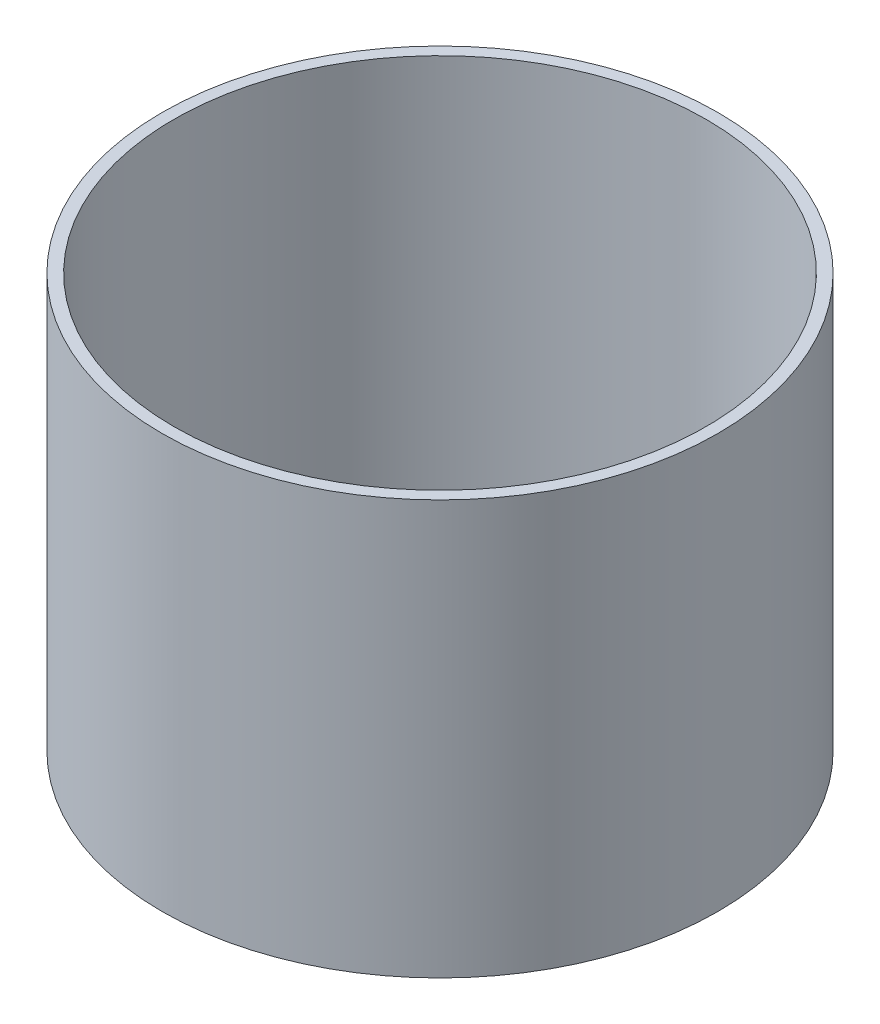
SolidWorks part; units mm, degrees
ref_plane "Front Plane" through (0, 0, 0) normal (0, 0, 1) x (1, 0, 0)
ref_plane "Top Plane" through (0, 0, 0) normal (0, 1, 0) x (1, 0, 0)
ref_plane "Right Plane" through (0, 0, 0) normal (1, 0, 0) x (0, 0, -1)
sketch "Sketch3" plane through (0, 0, 0) normal (0, 1, 0) x (1, 0, 0)
  line L0 (0, 0) -> (114.3, 0) construction
  line L1 (0, 0) -> (0, 114.3) construction
  line L2 (34.925, 38.1) -> (-34.925, 38.1)
  line L3 (34.925, 38.1) -> (34.925, 76.2)
  line L4 (34.925, 76.2) -> (-34.925, 76.2)
  line L5 (-34.925, 38.1) -> (-34.925, 76.2)
  line L6 (34.925, 38.1) -> (-34.925, 76.2) construction
  line L7 (34.925, 76.2) -> (-34.925, 38.1) construction
  line L8 (34.925, -76.2) -> (-34.925, -76.2)
  line L9 (-34.925, -38.1) -> (-34.925, -76.2)
  line L10 (34.925, -38.1) -> (-34.925, -38.1)
  line L11 (34.925, -38.1) -> (34.925, -76.2)
  line L12 (114.3, 0) -> (88.9, 0) construction
  line L14 (76.962, 14.986) -> (100.838, 14.986) construction
  line L15 (76.962, 14.986) -> (76.962, -14.986) construction
  line L16 (76.962, -14.986) -> (100.838, -14.986) construction
  line L17 (100.838, 14.986) -> (100.838, -14.986) construction
  line L18 (76.962, 14.986) -> (100.838, -14.986) construction
  line L19 (76.962, -14.986) -> (100.838, 14.986) construction
  circle A0 centre (0, 0) radius 114.3
  circle A1 centre (0, 0) radius 119.38
  circle A3 centre (76.962, 14.986) radius 1.778
  circle A4 centre (100.838, 14.986) radius 1.778
  circle A5 centre (76.962, -14.986) radius 1.778
  circle A6 centre (100.838, -14.986) radius 1.778
  point P5 (0, 57.15)
  dimension "D1" = 228.6
  dimension "D3" = 69.85
  dimension "D4" = 38.1
  dimension "D5" = 25.4
  dimension "D6" = 23.876
  dimension "D7" = 29.972
  dimension "D2" = 5.08
extrude "Boss-Extrude1" add sketch "Sketch3" along normal blind 177.8 contours A1 | A0
